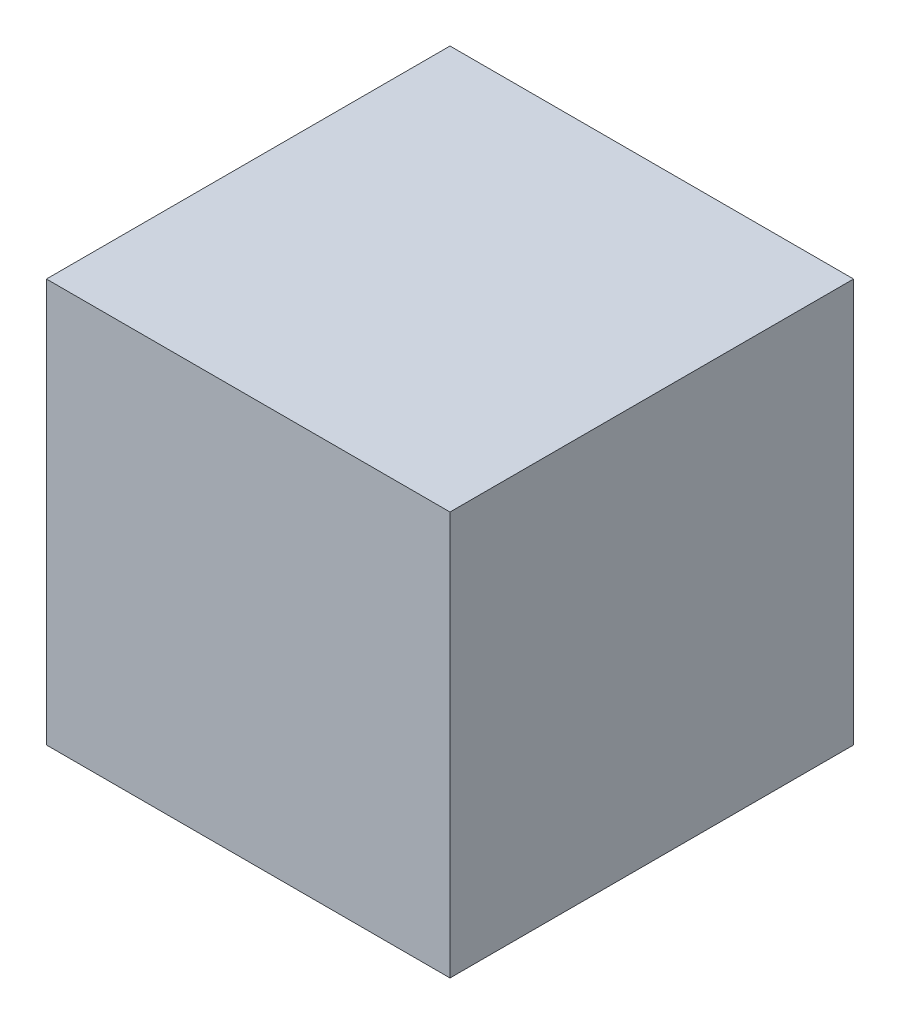
SolidWorks part; units mm, degrees
ref_plane "Plan de face" through (0, 0, 0) normal (0, 0, 1) x (1, 0, 0)
ref_plane "Plan de dessus" through (0, 0, 0) normal (0, 1, 0) x (1, 0, 0)
ref_plane "Plan de droite" through (0, 0, 0) normal (1, 0, 0) x (0, 0, -1)
sketch "Esquisse1" plane through (0, 0, 0) normal (0, 1, 0) x (1, 0, 0)
  line L1 (0, 0) -> (22, 0)
  line L2 (0, 0) -> (0, 22)
  line L3 (0, 22) -> (22, 22)
  line L4 (22, 0) -> (22, 22)
  dimension "D1" = 22
extrude "Extrusion1" add sketch "Esquisse1" along normal blind 22
